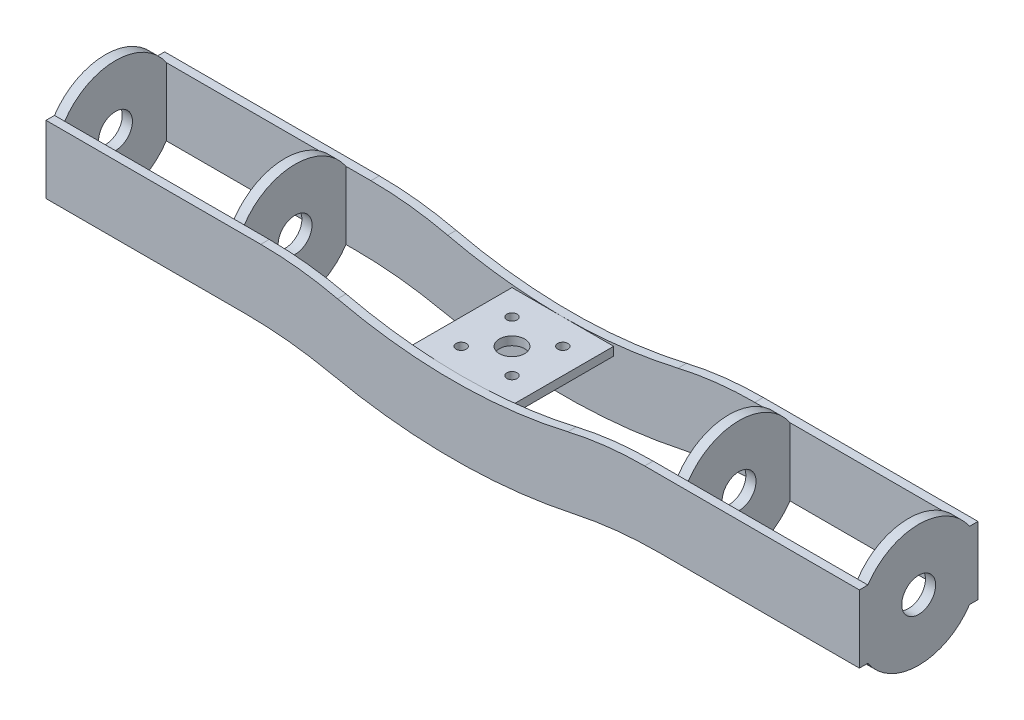
SolidWorks part; units mm, degrees
ref_plane "Front Plane" through (0, 0, 0) normal (0, 0, 1) x (1, 0, 0)
ref_plane "Top Plane" through (0, 0, 0) normal (0, 1, 0) x (1, 0, 0)
ref_plane "Right Plane" through (0, 0, 0) normal (1, 0, 0) x (0, 0, -1)
sketch "Sketch1" plane through (0, 0, 0) normal (0, 0, 1) x (1, 0, 0)
  line L0 (-120, 0) -> (-61.0553, 0)
  line L1 (-120, 0) -> (-120, 20)
  line L2 (-120, 20) -> (-56.637, 20)
  line L3 (120, 20) -> (120, 0)
  line L4 (0, 163.5) -> (0, 0) construction
  line L5 (56.637, 20) -> (120, 20)
  line L6 (61.0553, 0) -> (120, 0)
  arc A0 (-35.791, -2.6897) -> (35.791, -2.6897) centre (0, 163.5) ccw
  arc A1 (-33.9822, 17.4) -> (33.9822, 17.4) centre (0, 163.5) ccw
  arc A2 (33.9822, 17.4) -> (56.637, 20) centre (56.637, -80) cw
  arc A3 (-33.9822, 17.4) -> (-56.637, 20) centre (-56.637, -80) ccw
  arc A4 (35.791, -2.6897) -> (61.0553, 0) centre (61.0553, -120) cw
  arc A5 (-35.791, -2.6897) -> (-61.0553, 0) centre (-61.0553, -120) ccw
  point P9 (0, -6.5)
  point P17 (43.6778, 20)
  point P23 (46.5591, 0)
  dimension "D3" = 20
  dimension "D4" = 300
  dimension "D7" = 100
  dimension "D8" = 120
  dimension "D1" = 240
  dimension "D2" = 20
  dimension "D5" = 163.5
  dimension "D6" = 120
  dimension "D9" = 20
extrude "Boss-Extrude2" add sketch "Sketch1" along normal blind 2.5
ref_plane "Plane3" through (0, 0, -15) normal (0, 0, 1) x (1, 0, 0)
mirror "Mirror7" about plane through (0, 0, -15) normal (0, 0, 1) of bodies 103
sketch "Sketch2" plane through (120, 0, 0) normal (1, 0, 0) x (0, 0, -1)
  line L0 (30, 0) -> (30, 20) construction
  line L2 (0, 20) -> (0, 0)
  line L3 (30, 20) -> (30, 0)
  arc A0 (0, 0) -> (30, 0) centre (15, 10) ccw
  circle A1 centre (15, 10) radius 5
  arc A2 (30, 20) -> (0, 20) centre (15, 10) ccw
  point P6 (30, 10)
  dimension "D1" = 10
extrude "Boss-Extrude3" add sketch "Sketch2" against normal blind 3
ref_plane "Plane4" through (67, 0, 0) normal (-1, 0, 0) x (0, 0, 1)
pattern_linear "LPattern1" count 2 spacing 53 along (-1, 0, 0) of "Boss-Extrude3"
mirror "Mirror8" about plane through (0, 0, 0) normal (1, 0, 0) of "LPattern1", "Boss-Extrude3"
sketch "Sketch4" plane through (0, 0, -32.5) normal (0, 0, -1) x (-1, 0, 0)
  line L1 (-15, 13.5) -> (15, 13.5)
  line L2 (-15, 13.5) -> (-15, 11)
  line L3 (-15, 11) -> (15, 11)
  line L4 (15, 13.5) -> (15, 11)
  line L5 (-15, 13.5) -> (15, 11) construction
  line L6 (-15, 11) -> (15, 13.5) construction
  arc A0 (-33.9822, 17.4) -> (33.9822, 17.4) centre (0, 163.5) ccw construction
  point P0 (0, 12.25)
  dimension "D1" = 30
  dimension "D2" = 2.5
extrude "Boss-Extrude4" add sketch "Sketch4" against normal up to vertex (35 mm away)
sketch "Sketch6" plane through (0, 13.5, 0) normal (0, 1, 0) x (1, 0, 0)
  line L0 (15, 0) -> (15, 30) construction
  line L1 (-7.5, 22.5) -> (7.5, 7.5) construction
  circle A0 centre (0, 15) radius 3.75
  circle A1 centre (-7.5, 22.5) radius 1.5
  circle A2 centre (7.5, 22.5) radius 1.5
  circle A3 centre (7.5, 7.5) radius 1.5
  circle A4 centre (-7.5, 7.5) radius 1.5
  point P10 (0, 15)
  point P18 (15, 15)
  dimension "D1" = 3
  dimension "D2" = 7.5
  dimension "D3" = 15
  dimension "D6" = 15
extrude "Cut-Extrude1" cut sketch "Sketch6" against normal up to vertex (2.5 mm away)
